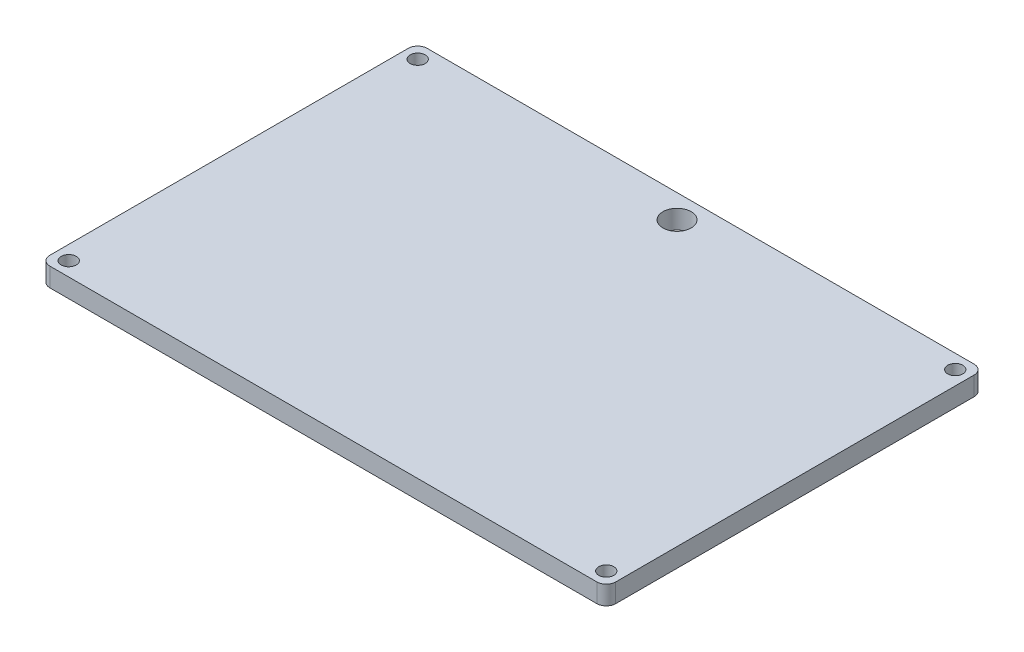
SolidWorks part; units mm, degrees
ref_plane "Front Plane" through (0, 0, 0) normal (0, 0, 1) x (1, 0, 0)
ref_plane "Top Plane" through (0, 0, 0) normal (0, 1, 0) x (1, 0, 0)
ref_plane "Right Plane" through (0, 0, 0) normal (1, 0, 0) x (0, 0, -1)
sketch "Sketch1" plane through (0, 0, 0) normal (0, 1, 0) x (1, 0, 0)
  line L0 (3, 80) -> (3, 77) construction
  line L1 (0, 0) -> (120, 0)
  line L2 (0, 0) -> (0, 80)
  line L3 (0, 80) -> (120, 80)
  line L4 (120, 0) -> (120, 80)
  line L5 (3, 77) -> (0, 77) construction
  line L6 (0, 3) -> (3, 3) construction
  line L7 (3, 3) -> (3, 0) construction
  line L8 (117, 80) -> (117, 77) construction
  line L9 (117, 77) -> (120, 77) construction
  line L10 (120, 3) -> (117, 3) construction
  line L11 (117, 3) -> (117, 0) construction
  line L12 (0, 40) -> (120, 40) construction
  line L13 (60, 80) -> (60, 0) construction
  line L20 (3, 80) -> (3, 0) construction
  line L28 (0, 3) -> (120, 3) construction
  line L34 (117, 80) -> (117, 0) construction
  line L39 (110, 59) -> (120, 59) construction
  circle A0 centre (3, 77) radius 1.6
  circle A1 centre (3, 3) radius 1.6
  circle A2 centre (117, 77) radius 1.6
  circle A3 centre (117, 3) radius 1.6
  circle A23 centre (60, 75) radius 3
  dimension "D5" = 3.2
  dimension "D8" = 3.2
  dimension "D11" = 3.2
  dimension "D14" = 3.2
  dimension "D16" = 5
  dimension "D15" = 6
  dimension "D1" = 80
  dimension "D2" = 120
  dimension "D3" = 3
  dimension "D4" = 3
  dimension "D6" = 3
  dimension "D7" = 3
  dimension "D9" = 3
  dimension "D10" = 3
  dimension "D12" = 3
  dimension "D13" = 3
extrude "Boss-Extrude1" add sketch "Sketch1" along normal blind 4
fillet "Fillet1" radius 2 1 edges at (0, 2, 0)
fillet "Fillet2" radius 2 1 edges at (120, 2, 0)
fillet "Fillet3" radius 2 1 edges at (120, 2, -80)
fillet "Fillet4" radius 2 1 edges at (0, 2, -80)
